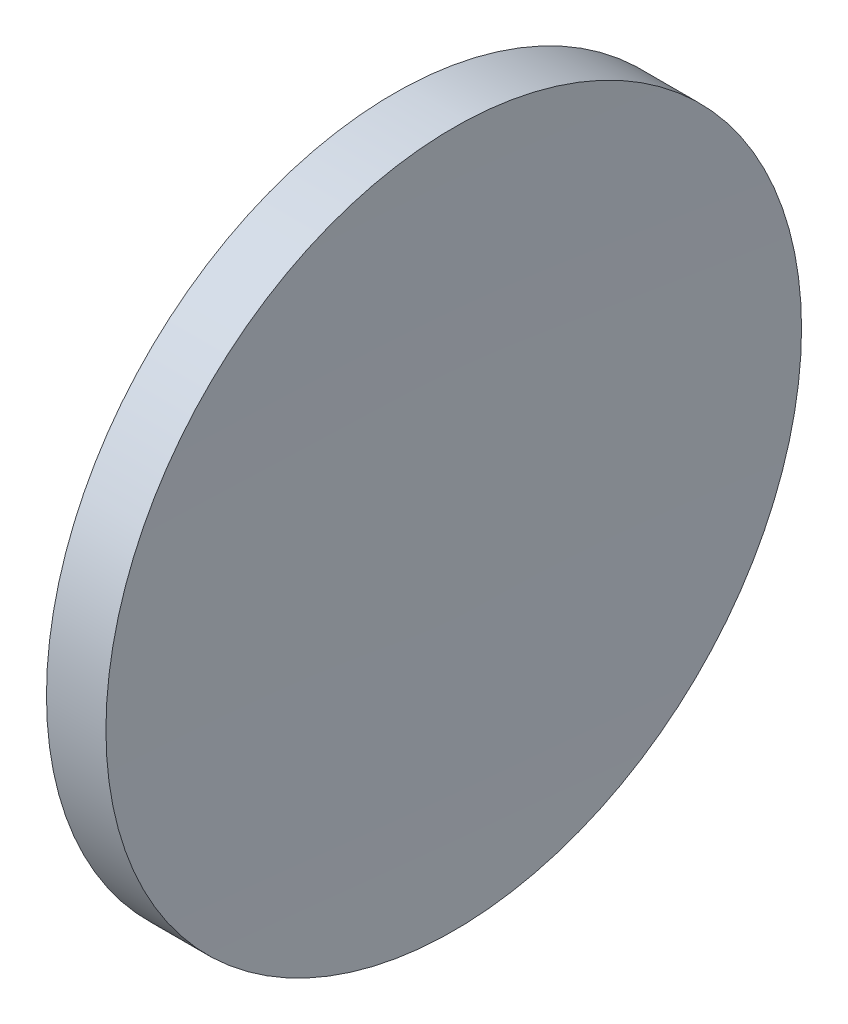
SolidWorks part; units mm, degrees
ref_plane "前视基准面" through (0, 0, 0) normal (0, 0, 1) x (1, 0, 0)
ref_plane "上视基准面" through (0, 0, 0) normal (0, 1, 0) x (1, 0, 0)
ref_plane "右视基准面" through (0, 0, 0) normal (1, 0, 0) x (0, 0, -1)
sketch "草图1" plane through (0, 0, 0) normal (0, 0, 1) x (1, 0, 0)
  line L0 (56.1009, 32.6108) -> (68.2773, 32.6108) construction
  line L1 (57.5323, 32.6108) -> (57.5323, 45.1108)
  line L2 (57.5323, 45.1108) -> (59.6694, 45.1108)
  line L3 (59.5323, 32.6108) -> (57.5323, 32.6108)
  arc A0 (59.6694, 45.1108) -> (59.5323, 32.6108) centre (576.032, 33.1989) ccw
revolve "旋转1" add sketch "草图1" angle 360 about L0
